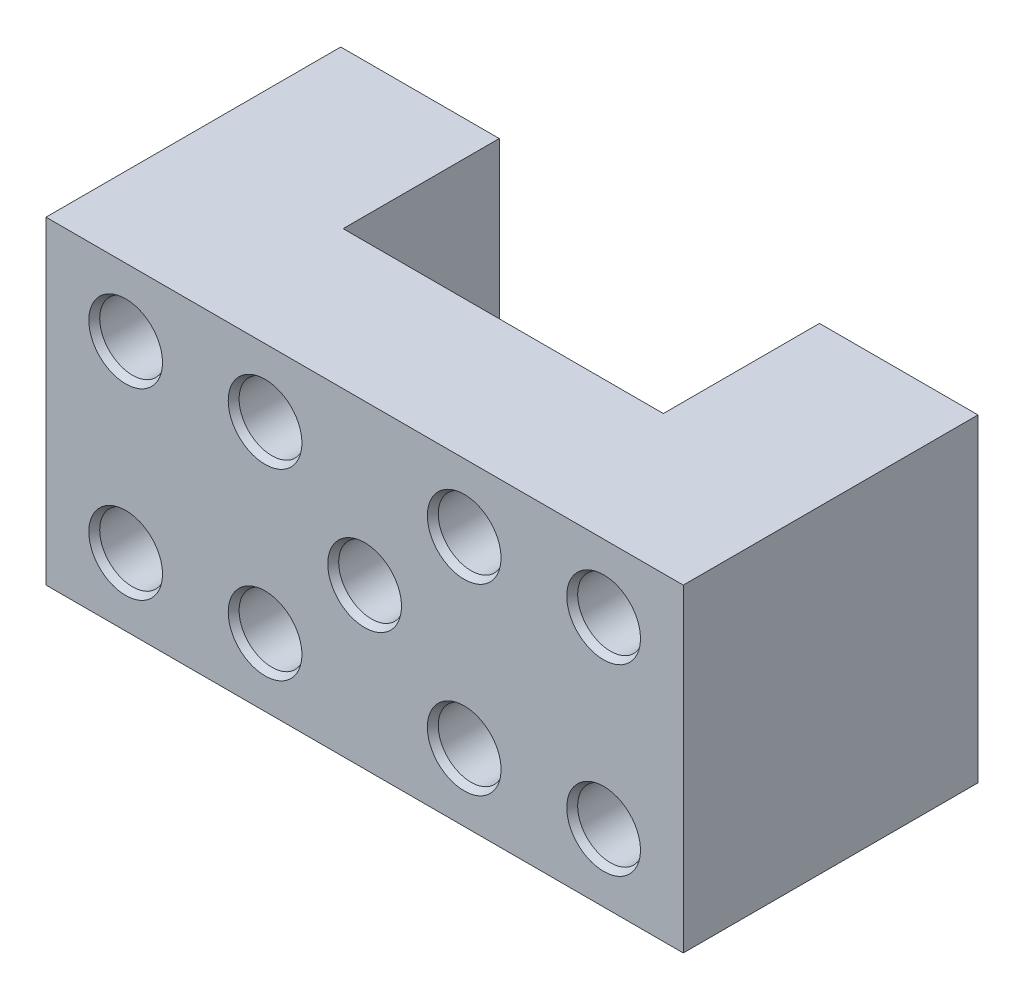
SolidWorks part; units mm, degrees
ref_plane "Спереди" through (0, 0, 0) normal (0, 0, 1) x (1, 0, 0)
ref_plane "Сверху" through (0, 0, 0) normal (0, 1, 0) x (1, 0, 0)
ref_plane "Справа" through (0, 0, 0) normal (1, 0, 0) x (0, 0, -1)
sketch "Sketch2" plane through (0, 0, 0) normal (0, 1, 0) x (1, 0, 0)
  line L0 (-31.3121, 37) -> (-31.3121, 0)
  line L1 (-31.3121, 0) -> (48.6879, 0)
  line L2 (48.6879, 0) -> (48.6879, 37)
  line L3 (48.6879, 37) -> (28.7879, 37)
  line L4 (28.7879, 37) -> (28.7879, 17.4)
  line L5 (28.7879, 17.4) -> (-11.4121, 17.4)
  line L6 (-11.4121, 17.4) -> (-11.4121, 37)
  line L7 (-11.4121, 37) -> (-31.3121, 37)
  dimension "D1" = 80
  dimension "D2" = 40.2
  dimension "D3" = 37
  dimension "D4" = 19.6
extrude "Boss-Extrude2" add sketch "Sketch2" along normal blind 40
sketch "Sketch3" plane through (0, 0, 0) normal (0, 0, 1) x (1, 0, 0)
  line L0 (8.6879, 40) -> (8.6879, 0) construction
  line L1 (-31.3121, 40) -> (48.6879, 40) construction
  line L2 (-31.3121, 0) -> (48.6879, 0) construction
  line L4 (21.1879, 8.5) -> (-3.8121, 8.5) construction
  line L5 (21.1879, 8.5) -> (21.1879, 31.5) construction
  line L6 (21.1879, 31.5) -> (-3.8121, 31.5) construction
  line L7 (-3.8121, 8.5) -> (-3.8121, 31.5) construction
  line L8 (21.1879, 8.5) -> (-3.8121, 31.5) construction
  line L9 (21.1879, 31.5) -> (-3.8121, 8.5) construction
  line L10 (38.6879, 8.5) -> (-21.3121, 8.5) construction
  line L11 (38.6879, 8.5) -> (38.6879, 31.5) construction
  line L12 (38.6879, 31.5) -> (-21.3121, 31.5) construction
  line L13 (-21.3121, 8.5) -> (-21.3121, 31.5) construction
  line L14 (38.6879, 8.5) -> (-21.3121, 31.5) construction
  line L15 (38.6879, 31.5) -> (-21.3121, 8.5) construction
  circle A0 centre (-3.8121, 31.5) radius 4.125
  circle A1 centre (21.1879, 31.5) radius 4.125
  circle A2 centre (21.1879, 8.5) radius 4.125
  circle A3 centre (-3.8121, 8.5) radius 4.125
  circle A4 centre (-21.3121, 31.5) radius 4.125
  circle A5 centre (38.6879, 31.5) radius 4.125
  circle A6 centre (38.6879, 8.5) radius 4.125
  circle A7 centre (-21.3121, 8.5) radius 4.125
  circle A8 centre (8.6879, 20) radius 4.125
  point P6 (8.6879, 20)
  point P15 (8.6879, 20)
  dimension "D2" = 8.25
  dimension "D1" = 25
  dimension "D3" = 60
  dimension "D4" = 23
extrude "Cut-Extrude1" cut sketch "Sketch3" against normal through all
chamfer "Chamfer1" distance 0.5 angle 60 9 edges at (25.3129, 8.5, 0) (42.8129, 8.5, 0) (42.8129, 31.5, 0) (25.3129, 31.5, 0) (0.3129, 31.5, 0) (12.8129, 20, 0) (0.3129, 8.5, 0) (-17.1871, 8.5, 0) (-17.1871, 31.5, 0)
